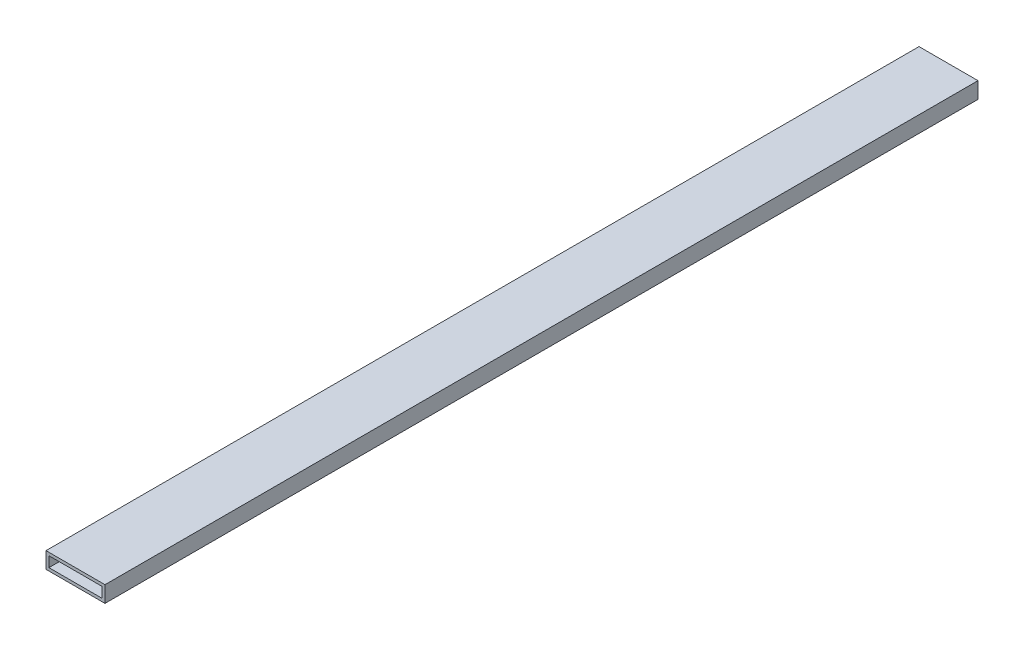
SolidWorks part; units mm, degrees
ref_plane "Front Plane" through (0, 0, 0) normal (0, 0, 1) x (1, 0, 0)
ref_plane "Top Plane" through (0, 0, 0) normal (0, 1, 0) x (1, 0, 0)
ref_plane "Right Plane" through (0, 0, 0) normal (1, 0, 0) x (0, 0, -1)
sketch "Sketch1" plane through (0, 0, 0) normal (0, 0, 1) x (1, 0, 0)
  line L0 (-18, 3.5) -> (18, 3.5)
  line L1 (-20, -5.5) -> (20, -5.5)
  line L2 (-20, -5.5) -> (-20, 5.5)
  line L3 (-20, 5.5) -> (20, 5.5)
  line L4 (20, -5.5) -> (20, 5.5)
  line L5 (-20, -5.5) -> (20, 5.5) construction
  line L6 (-20, 5.5) -> (20, -5.5) construction
  line L7 (18, -3.5) -> (18, 3.5)
  line L8 (-18, -3.5) -> (18, -3.5)
  line L9 (-18, -3.5) -> (-18, 3.5)
  point P0 (0, 0)
  dimension "D1" = 11
  dimension "D2" = 40
  dimension "D3" = 2
extrude "Boss-Extrude1" add sketch "Sketch1" along normal blind 592
